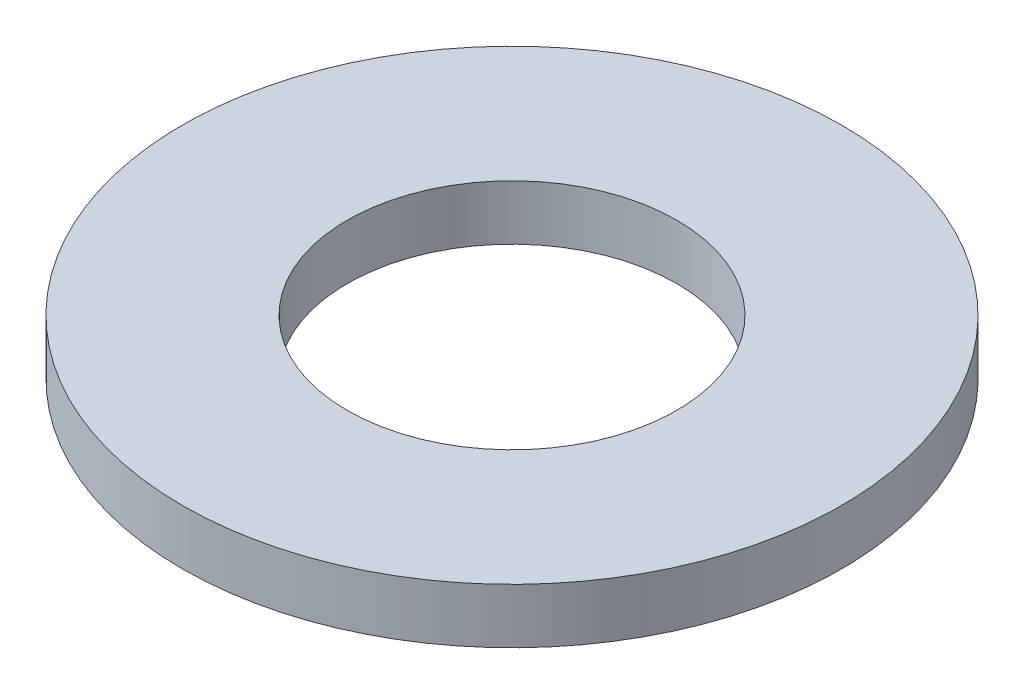
SolidWorks part; units mm, degrees
material "Brass"
ref_plane "Front Plane" through (0, 0, 0) normal (0, 0, 1) x (1, 0, 0)
ref_plane "Top Plane" through (0, 0, 0) normal (0, 1, 0) x (1, 0, 0)
ref_plane "Right Plane" through (0, 0, 0) normal (1, 0, 0) x (0, 0, -1)
sketch "Sketch1" plane through (0, 0, 0) normal (0, 1, 0) x (1, 0, 0)
  circle A0 centre (0, 0) radius 9.525
  circle A1 centre (0, 0) radius 4.7625
  dimension "D1" = 9.525
  dimension "D2" = 19.05
extrude "Boss-Extrude1" add sketch "Sketch1" along normal blind 1.5875
